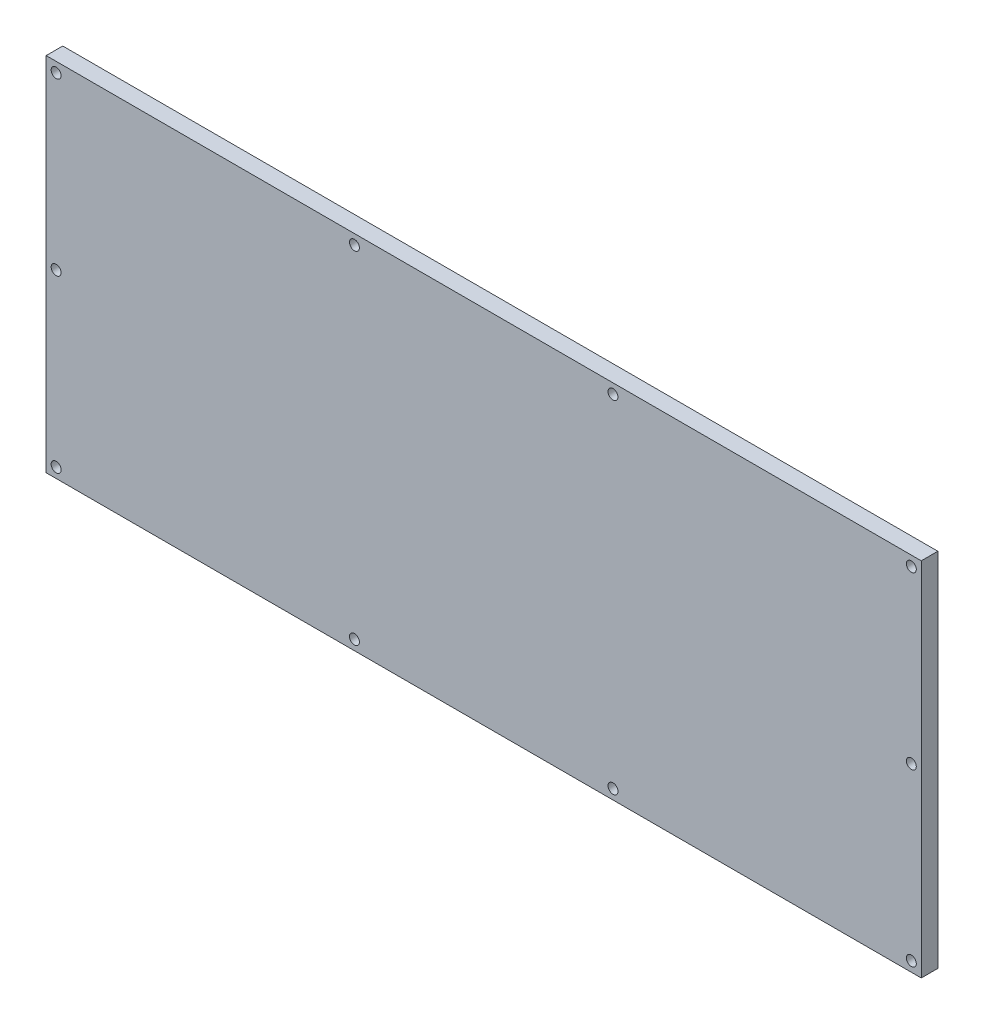
SolidWorks part; units mm, degrees
material "2014 Alloy"
ref_plane "Front Plane" through (0, 0, 0) normal (0, 0, 1) x (1, 0, 0)
ref_plane "Top Plane" through (0, 0, 0) normal (0, 1, 0) x (1, 0, 0)
ref_plane "Right Plane" through (0, 0, 0) normal (1, 0, 0) x (0, 0, -1)
sketch "Sketch1" plane through (0, 0, 0) normal (0, 0, 1) x (1, 0, 0)
  line L1 (-132, 54.5) -> (132, 54.5)
  line L2 (-132, 54.5) -> (-132, -54.5)
  line L3 (-132, -54.5) -> (132, -54.5)
  line L4 (132, 54.5) -> (132, -54.5)
  line L5 (-132, 54.5) -> (132, -54.5) construction
  line L6 (-132, -54.5) -> (132, 54.5) construction
  point P0 (0, 0)
  dimension "D1" = 264
  dimension "D2" = 109
extrude "Boss-Extrude1" add sketch "Sketch1" along normal blind 5
sketch "Sketch2" plane through (0, 0, 0) normal (0, 0, -1) x (-1, 0, 0)
  line L0 (121, 48.5) -> (-121, 48.5) construction
  line L1 (-126, 43.5) -> (-126, -43.5) construction
  line L2 (-121, -48.5) -> (121, -48.5) construction
  line L3 (126, -43.5) -> (126, 43.5) construction
  line L4 (132, 54.5) -> (132, -54.5) construction
  line L5 (-132, 54.5) -> (132, 54.5) construction
  line L6 (-132, -54.5) -> (-132, 54.5) construction
  line L8 (132, -54.5) -> (-132, -54.5) construction
  line L9 (121, 49.5) -> (-121, 49.5)
  line L10 (-127, 43.5) -> (-127, -43.5)
  line L11 (-121, -49.5) -> (121, -49.5)
  line L12 (127, -43.5) -> (127, 43.5)
  line L13 (121, 47.5) -> (-121, 47.5)
  line L14 (-125, 43.5) -> (-125, -43.5)
  line L15 (-121, -47.5) -> (121, -47.5)
  line L16 (125, -43.5) -> (125, 43.5)
  arc A0 (-126, -43.5) -> (-121, -48.5) centre (-121, -43.5) ccw construction
  arc A1 (-121, 48.5) -> (-126, 43.5) centre (-121, 43.5) ccw construction
  arc A2 (121, 48.5) -> (126, 43.5) centre (121, 43.5) cw construction
  arc A3 (126, -43.5) -> (121, -48.5) centre (121, -43.5) cw construction
  arc A4 (-121, 49.5) -> (-127, 43.5) centre (-121, 43.5) ccw
  arc A5 (-127, -43.5) -> (-121, -49.5) centre (-121, -43.5) ccw
  arc A6 (127, -43.5) -> (121, -49.5) centre (121, -43.5) cw
  arc A7 (121, 49.5) -> (127, 43.5) centre (121, 43.5) cw
  arc A8 (-121, 47.5) -> (-125, 43.5) centre (-121, 43.5) ccw
  arc A9 (-125, -43.5) -> (-121, -47.5) centre (-121, -43.5) ccw
  arc A10 (125, -43.5) -> (121, -47.5) centre (121, -43.5) cw
  arc A11 (121, 47.5) -> (125, 43.5) centre (121, 43.5) cw
  dimension "D5" = 5
  dimension "D1" = 6
  dimension "D2" = 6
  dimension "D3" = 6
  dimension "D4" = 6
  dimension "D6" = 1
  dimension "D7" = 1
extrude "Cut-Extrude1" cut sketch "Sketch2" against normal blind 1
sketch "Sketch3" plane through (0, 0, 0) normal (0, 0, -1) x (-1, 0, 0)
  line L0 (-117, 39.5) -> (-117, -37.2495)
  line L1 (-117, -37.2495) -> (115.8989, 39.5)
  line L2 (115.8989, 39.5) -> (-117, 39.5)
  line L3 (-91.8787, -39.5) -> (117, 29.3339)
  line L4 (117, 29.3339) -> (117, -39.5)
  line L5 (117, -39.5) -> (-91.8787, -39.5)
  line L6 (132, -54.5) -> (-132, -54.5) construction
  line L7 (-132, 54.5) -> (132, 54.5) construction
  line L8 (132, 54.5) -> (132, -54.5) construction
  line L9 (-132, -54.5) -> (-132, 54.5) construction
  dimension "D1" = 15
  dimension "D2" = 15
  dimension "D3" = 15
  dimension "D4" = 15
  dimension "D5" = 10
extrude "Cut-Extrude2" cut sketch "Sketch3" against normal blind 4
fillet "Fillet1" radius 3 6 edges at (-117, -39.5, 2) (91.8787, -39.5, 2) (-117, 29.3339, 2) (-115.8989, 39.5, 2) (117, 39.5, 2) (117, -37.2495, 2)
hole_wizard "Ø3.0mm Dowel Hole1" positions "Sketch5" profile "Sketch4" hole size "Ø3.0" standard "ISO"
sketch "Sketch5" plane through (0, 0, 0) normal (0, 0, -1) x (-1, 0, 0)
  line L0 (-132, -54.5) -> (-132, 54.5) construction
  line L1 (132, -54.5) -> (-132, -54.5) construction
  line L2 (132, 54.5) -> (132, -54.5) construction
  line L3 (-132, 54.5) -> (132, 54.5) construction
  point P0 (-129, -51.5)
  point P2 (-129, 51.5)
  point P4 (129, 51.5)
  point P6 (129, -51.5)
  point P18 (-39, -51.5)
  point P20 (39, -51.5)
  point P22 (39, 51.5)
  point P24 (-39, 51.5)
  point P31 (129, 0)
  point P33 (-129, 0)
  dimension "D1" = 3
  dimension "D2" = 3
  dimension "D3" = 3
  dimension "D4" = 3
  dimension "D5" = 90
  dimension "D6" = 90
sketch "Sketch4" plane through (129, -51.5, 0) normal (1, 0, 0) x (0, 1, 0)
  line L0 (0, 0) -> (0, 15.9013)
  line L1 (0, 15.9013) -> (1.5, 15)
  line L2 (1.5, 15) -> (1.5, 0)
  line L5 (1.5, 0) -> (0, 0)
  line L10 (0, 15.9013) -> (-1.5, 15) construction
  line L11 (0, -6.35) -> (0, 107.95) construction
  dimension "Hole Dia." = 3
  dimension "Hole Depth" = 15
  dimension "Drill Angle" = 118
